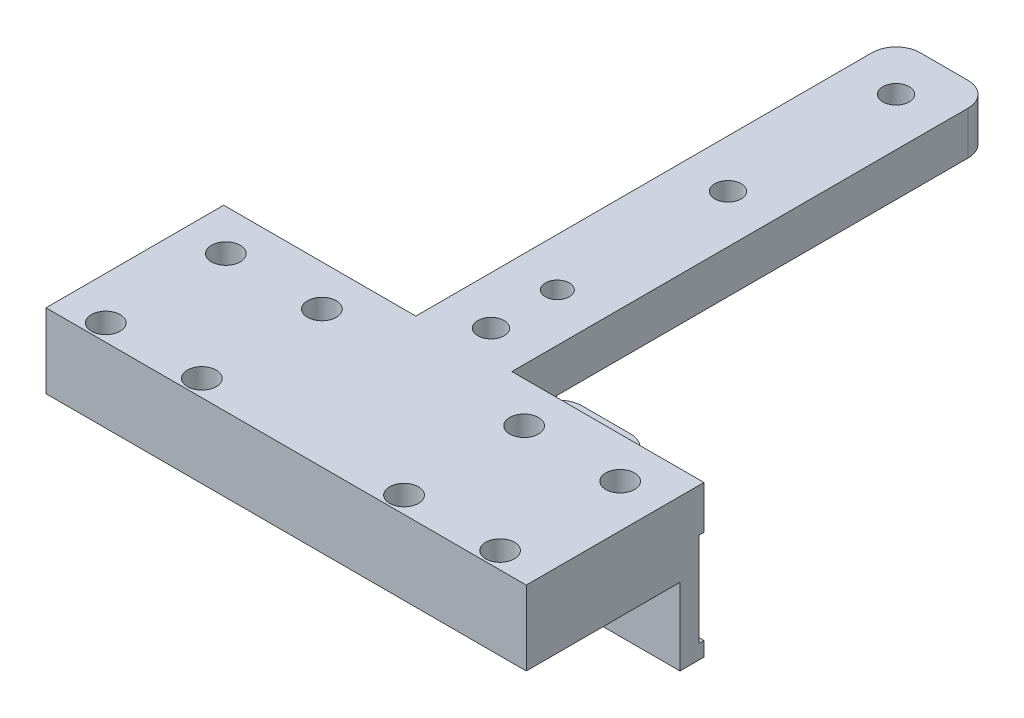
SolidWorks part; units mm, degrees
ref_plane "Front Plane" through (0, 0, 0) normal (0, 0, 1) x (1, 0, 0)
ref_plane "Top Plane" through (0, 0, 0) normal (0, 1, 0) x (1, 0, 0)
ref_plane "Right Plane" through (0, 0, 0) normal (1, 0, 0) x (0, 0, -1)
sketch "Sketch1" plane through (0, 0, 0) normal (0, 1, 0) x (1, 0, 0)
  line L1 (0, 0) -> (100, 0)
  line L2 (0, 0) -> (0, 37)
  line L3 (0, 37) -> (100, 37)
  line L4 (100, 0) -> (100, 37)
  dimension "D1" = 100
  dimension "D2" = 37
extrude "Boss-Extrude1" add sketch "Sketch1" along normal blind 6
sketch "Sketch2" plane through (0, 0, 0) normal (0, -1, 0) x (1, 0, 0)
  circle A0 centre (71.05, -3.5) radius 1.2295 construction
  circle A1 centre (71.05, -3.5) radius 1.2295 construction
  circle A2 centre (71.05, -28.5) radius 1.2295 construction
  circle A3 centre (71.05, -28.5) radius 1.2295 construction
  circle A4 centre (91.05, -28.5) radius 1.2295 construction
  circle A5 centre (91.05, -28.5) radius 1.2295 construction
  circle A6 centre (91.05, -3.5) radius 1.2295 construction
  circle A7 centre (91.05, -3.5) radius 1.2295 construction
  circle A8 centre (28.95, -28.5) radius 1.2295 construction
  circle A9 centre (28.95, -28.5) radius 1.2295 construction
  circle A10 centre (28.95, -3.5) radius 1.2295 construction
  circle A11 centre (28.95, -3.5) radius 1.2295 construction
  circle A12 centre (8.95, -3.5) radius 1.2295 construction
  circle A13 centre (8.95, -3.5) radius 1.2295 construction
  circle A14 centre (8.95, -28.5) radius 1.2295 construction
  circle A15 centre (8.95, -28.5) radius 1.2295 construction
  circle A16 centre (71.05, -3.5) radius 1.2295
  circle A17 centre (71.05, -3.5) radius 1.2295
  circle A18 centre (71.05, -28.5) radius 1.2295
  circle A19 centre (71.05, -28.5) radius 1.2295
  circle A20 centre (91.05, -28.5) radius 1.2295
  circle A21 centre (91.05, -28.5) radius 1.2295
  circle A22 centre (91.05, -3.5) radius 1.2295
  circle A23 centre (91.05, -3.5) radius 1.2295
  circle A24 centre (28.95, -28.5) radius 1.2295
  circle A25 centre (28.95, -28.5) radius 1.2295
  circle A26 centre (28.95, -3.5) radius 1.2295
  circle A27 centre (28.95, -3.5) radius 1.2295
  circle A28 centre (8.95, -3.5) radius 1.2295
  circle A29 centre (8.95, -3.5) radius 1.2295
  circle A30 centre (8.95, -28.5) radius 1.2295
  circle A31 centre (8.95, -28.5) radius 1.2295
ref_plane "Plane1" through (50, 0, 0) normal (1, 0, 0) x (0, 0, -1)
ref_plane "Plane2" through (0, 0, -16) normal (0, 0, 1) x (1, 0, 0)
hole_wizard "M3 Clearance Hole1" positions "Sketch3" profile "Sketch4" hole size "M3" standard "ANSI Metric" end condition through all
sketch "Sketch3" plane through (0, 0, 0) normal (0, -1, 0) x (-1, 0, 0)
  point P0 (-8.95, 3.5)
  point P3 (-8.95, 28.5)
  point P6 (-28.95, 28.5)
  point P9 (-28.95, 3.5)
  point P12 (-71.05, 3.5)
  point P15 (-71.05, 28.5)
  point P18 (-91.05, 28.5)
  point P21 (-91.05, 3.5)
sketch "Sketch4" plane through (8.95, 0, -3.5) normal (1, 0, 0) x (0, 0, -1)
  line L0 (0, 0) -> (0, 6)
  line L1 (0, 6) -> (1.7, 6)
  line L2 (1.7, 6) -> (1.7, 0)
  line L5 (1.7, 0) -> (0, 0)
  line L11 (0, -6.35) -> (0, 107.95) construction
  dimension "Thru Hole Dia." = 3.4
  dimension "Thru Hole Depth" = 6
sketch "Sketch30" plane through (0, 0, 0) normal (0, -1, 0) x (1, 0, 0)
  line L0 (50, -37) -> (50, 0) construction
  line L1 (100, -37) -> (0, -37) construction
  line L2 (0, 0) -> (100, 0) construction
  line L3 (50, -37) -> (50, -56.47) construction
  circle A0 centre (50, -56.47) radius 2.5
  point P6 (0, 0)
  point P10 (50.5116, -56.47)
  point P11 (50, -56.47)
  point P12 (0, 0)
  dimension "D1" = 5
  dimension "D2" = 19.47
sketch "Sketch31" plane through (0, 0, 0) normal (0, -1, 0) x (1, 0, 0)
  line L0 (40, -37) -> (40, -66.63)
  line L1 (100, -37) -> (0, -37) construction
  line L2 (40, -66.63) -> (60, -66.63)
  line L3 (60, -66.63) -> (60, -37)
  line L4 (60, -37) -> (40, -37)
  line L6 (50, -56.47) -> (50, -66.63) construction
  point P13 (0, 0)
  point P14 (0, 0)
  dimension "D1" = 10
  dimension "D2" = 10.16
extrude "Boss-Extrude9" add sketch "Sketch31" against normal offset from surface 3 and the other way blind 16 up to face at (8.95, 6, -5.2) offset beyond the face yes
sketch "Sketch32" plane through (0, 0, 0) normal (0, -1, 0) x (1, 0, 0)
  line L0 (0, -37) -> (0, 0) construction
  line L1 (0, -32) -> (100, -32)
  line L2 (0, -32) -> (0, -37)
  line L3 (0, -37) -> (100, -37)
  line L4 (100, -32) -> (100, -37)
  dimension "D1" = 5
extrude "Boss-Extrude10" add sketch "Sketch32" along normal up to surface (16 mm away) up to face at (50, -16, -51.815)
sketch "Sketch33" plane through (0, 6, 0) normal (0, 1, 0) x (1, 0, 0)
  line L6 (0, 37) -> (0, 0)
  line L7 (0, 0) -> (100, 0)
  line L8 (100, 0) -> (100, 37)
  line L9 (100, 37) -> (60, 37)
  line L10 (60, 37) -> (40, 37)
  line L11 (40, 37) -> (0, 37)
  line L12 (0, 37) -> (0, 0)
  line L13 (0, 0) -> (100, 0)
  line L14 (100, 0) -> (100, 37)
  line L15 (100, 37) -> (60, 37)
  line L16 (60, 37) -> (40, 37)
  line L17 (40, 37) -> (0, 37)
  circle A0 centre (71.05, 3.5) radius 3
  circle A1 centre (71.05, 28.5) radius 3
  circle A2 centre (28.95, 3.5) radius 3
  circle A3 centre (28.95, 28.5) radius 3
  circle A4 centre (8.95, 28.5) radius 3
  circle A5 centre (8.95, 3.5) radius 3
  circle A6 centre (91.05, 3.5) radius 3
  circle A7 centre (91.05, 28.5) radius 3
  dimension "D2" = 6
  dimension "D1" = 0
extrude "Boss-Extrude11" add sketch "Sketch33" along normal up to surface (3 mm away) up to face at (50, 9, -51.815)
sketch "Sketch34" plane through (100, 0, 0) normal (1, 0, 0) x (0, 0, -1)
  line L0 (37, -16) -> (32, -16) construction
  line L1 (36, 6.5) -> (39, 6.5)
  line L2 (36, 6.5) -> (36, -13)
  line L3 (36, -13) -> (39, -13)
  line L4 (39, 6.5) -> (39, -13)
  line L5 (37, 9) -> (37, -16) construction
  dimension "D1" = 19.5
  dimension "D2" = 3
  dimension "D3" = 1
  dimension "D4" = 3
extrude "Cut-Extrude1" cut sketch "Sketch34" against normal through all
sketch "Sketch35" plane through (0, 9, 0) normal (0, 1, 0) x (1, 0, 0)
  line L11 (60, 37) -> (60, 39) construction
  line L12 (40, 66.63) -> (60, 66.63)
  line L13 (40, 66.63) -> (40, 46.31)
  line L14 (40, 46.31) -> (60, 46.31)
  line L15 (60, 66.63) -> (60, 46.31)
  line L16 (40, 66.63) -> (60, 46.31) construction
  line L17 (40, 46.31) -> (60, 66.63) construction
  line L18 (60, 66.63) -> (40, 66.63) construction
  point P0 (50, 56.47)
  point P5 (0, 0)
extrude "Cut-Extrude2" cut sketch "Sketch35" against normal up to surface (19.5 mm away) from offset 2.5 up to face at (50, -13, -37.25) offset against normal yes
sketch "Sketch36" plane through (0, 9, 0) normal (0, 1, 0) x (1, 0, 0)
  circle A0 centre (50, 56.47) radius 2.5 construction
  circle A2 centre (50, 56.47) radius 2.5
extrude "Cut-Extrude3" cut sketch "Sketch36" against normal through all
fillet "Fillet1" radius 5 4 edges at (40, -14.5, -66.63) (40, 7.75, -66.63) (60, -14.5, -66.63) (60, 7.75, -66.63)
sketch "Sketch37" plane through (0, 9, 0) normal (0, 1, 0) x (1, 0, 0)
  line L0 (40, 37) -> (0, 37)
  line L1 (100, 0) -> (0, 0)
  line L2 (100, 0) -> (100, 37)
  line L3 (100, 37) -> (60, 37)
  line L4 (0, 0) -> (0, 37)
  line L6 (40, 37) -> (40, 137)
  line L7 (40, 137) -> (60, 137)
  line L8 (60, 37) -> (60, 137)
  line L9 (50, 0) -> (50, 137) construction
  circle A0 centre (28.95, 3.5) radius 3 construction
  circle A1 centre (8.95, 3.5) radius 3 construction
  circle A2 centre (8.95, 28.5) radius 3 construction
  circle A3 centre (28.95, 28.5) radius 3 construction
  circle A4 centre (71.05, 28.5) radius 3 construction
  circle A5 centre (91.05, 28.5) radius 3 construction
  circle A6 centre (91.05, 3.5) radius 3 construction
  circle A7 centre (71.05, 3.5) radius 3 construction
  circle A8 centre (28.95, 3.5) radius 3
  circle A9 centre (8.95, 3.5) radius 3
  circle A10 centre (8.95, 28.5) radius 3
  circle A11 centre (28.95, 28.5) radius 3
  circle A12 centre (71.05, 28.5) radius 3
  circle A13 centre (91.05, 28.5) radius 3
  circle A14 centre (91.05, 3.5) radius 3
  circle A15 centre (71.05, 3.5) radius 3
  circle A16 centre (50, 56.47) radius 2.5 construction
  circle A17 centre (50, 56.47) radius 2.5
  dimension "D1" = 100
  dimension "D2" = 20
extrude "Boss-Extrude12" add sketch "Sketch37" along normal blind 6.5 and the other way blind 2.5
sketch "Sketch46" plane through (0, 6.5, 0) normal (0, -1, 0) x (1, 0, 0)
  line L0 (60, -127) -> (40, -127) construction
  line L1 (60, -46.31) -> (60, -137) construction
  line L2 (40, -137) -> (40, -46.31) construction
  line L3 (60, -137) -> (40, -137) construction
  line L4 (50, -127) -> (50, -92) construction
  line L5 (60, -92) -> (40, -92) construction
  point P12 (0, 0)
  point P13 (0, 0)
  dimension "D1" = 10
  dimension "D2" = 35
hole_wizard "CBORE for M5 SHCS1" positions "Sketch41" profile "Sketch42" counterbore size "M5" standard "ANSI Metric" end condition through all
sketch "Sketch41" plane through (0, -16, 0) normal (0, -1, 0) x (-1, 0, 0)
  line L1 (-60, 127) -> (-40, 127) construction
  point P3 (-50, 127)
  point P21 (-50, 92)
  point P25 (0, 0)
sketch "Sketch42" plane through (50, -16, -127) normal (1, 0, 0) x (0, 0, -1)
  line L0 (0, 0) -> (0, 31.5)
  line L1 (0, 31.5) -> (2.75, 31.5)
  line L3 (2.75, 31.5) -> (2.75, 26)
  line L4 (2.75, 26) -> (5, 26)
  line L5 (5, 26) -> (5, 0)
  line L7 (5, 0) -> (0, 0)
  line L11 (0, -6.35) -> (0, 107.95) construction
  dimension "Thru Hole Dia." = 5.5
  dimension "Thru Hole Depth" = 31.5
  dimension "C'Bore Dia." = 10
  dimension "C'Bore Depth" = 26
sketch "Sketch43" plane through (0, -16, 0) normal (0, -1, 0) x (1, 0, 0)
  line L0 (40, -39) -> (60, -39) construction
  line L1 (40, -46.31) -> (60, -46.31) construction
  line L2 (40, -39) -> (60, -39)
  line L3 (40, -46.31) -> (60, -46.31)
  line L4 (50, -39) -> (50, -46.31) construction
hole_wizard "M5 Clearance Hole1" positions "Sketch44" profile "Sketch45" hole size "M5" standard "ANSI Metric" end condition through all
sketch "Sketch44" plane through (0, -16, 0) normal (0, -1, 0) x (-1, 0, 0)
  line L0 (-50, 39) -> (-50, 46.31) construction
  point P0 (-50, 42.655)
  point P5 (0, 0)
sketch "Sketch45" plane through (50, -16, -42.655) normal (1, 0, 0) x (0, 0, -1)
  line L0 (0, 0) -> (0, 31.5)
  line L1 (0, 31.5) -> (2.75, 31.5)
  line L2 (2.75, 31.5) -> (2.75, 0)
  line L5 (2.75, 0) -> (0, 0)
  line L11 (0, -6.35) -> (0, 107.95) construction
  dimension "Thru Hole Dia." = 5.5
  dimension "Thru Hole Depth" = 31.5
fillet "Fillet3" radius 5 2 edges at (40, 11, -137) (60, 11, -137)
sketch "Sketch48" plane through (0, 0, 0) normal (0, -1, 0) x (1, 0, 0)
  line L0 (0, -36) -> (100, -36) construction
  line L1 (55.6008, -36) -> (44.3992, -36)
  line L2 (55.6008, -36) -> (55.6008, -26)
  line L3 (55.6008, -26) -> (44.3992, -26)
  line L4 (44.3992, -36) -> (44.3992, -26)
  line L7 (50, -36) -> (50, -56.47) construction
  dimension "D1" = 10
  dimension "D2" = 11.2016
extrude "Boss-Extrude15" add sketch "Sketch48" along normal blind 14
